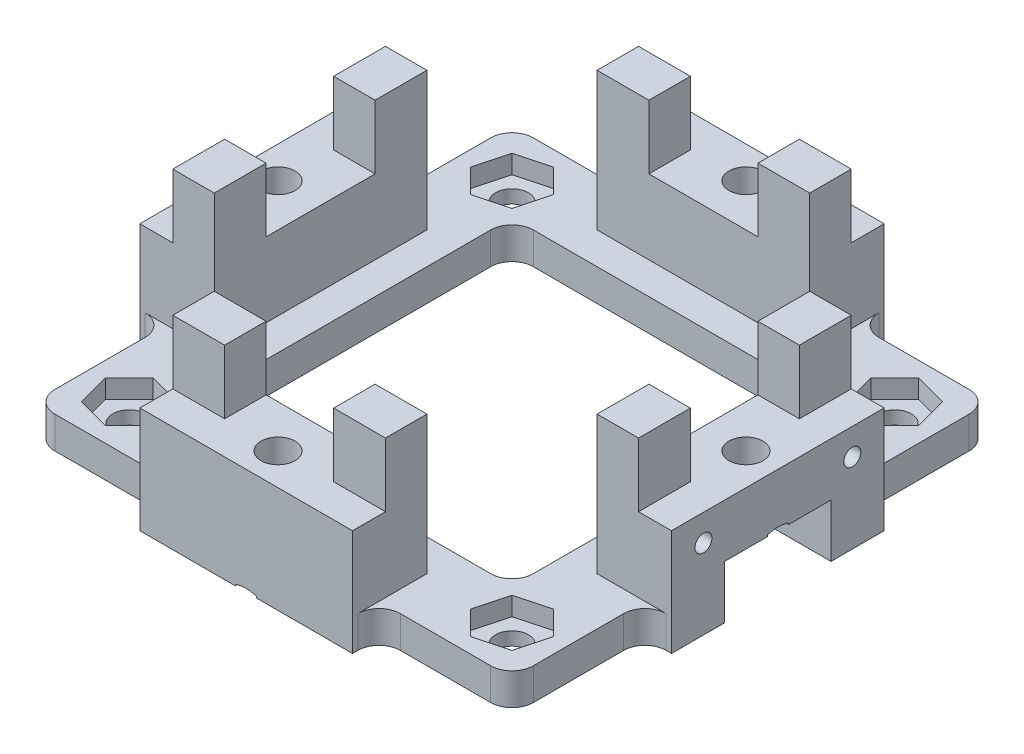
SolidWorks part; units mm, degrees
ref_plane "Front Plane" through (0, 0, 0) normal (0, 0, 1) x (1, 0, 0)
ref_plane "Top Plane" through (0, 0, 0) normal (0, 1, 0) x (1, 0, 0)
ref_plane "Right Plane" through (0, 0, 0) normal (1, 0, 0) x (0, 0, -1)
sketch "Sketch1" plane through (0, 0, 0) normal (0, 1, 0) x (1, 0, 0)
  line L0 (-10, 22.5) -> (-10, 25)
  line L1 (-15, -15) -> (15, -15)
  line L2 (-15, -15) -> (-15, 15)
  line L3 (-15, 15) -> (15, 15)
  line L4 (15, -15) -> (15, 15)
  line L5 (-15, -15) -> (15, 15) construction
  line L6 (-15, 15) -> (15, -15) construction
  line L7 (-22.5, -22.5) -> (-10, -22.5)
  line L8 (-22.5, -22.5) -> (-22.5, -10)
  line L9 (-22.5, 22.5) -> (-10, 22.5)
  line L10 (22.5, -22.5) -> (22.5, -10)
  line L11 (-22.5, -22.5) -> (22.5, 22.5) construction
  line L12 (-22.5, 22.5) -> (22.5, -22.5) construction
  line L13 (-10, 25) -> (10, 25)
  line L14 (10, 25) -> (10, 22.5)
  line L15 (0, 0) -> (0, 25) construction
  line L16 (22.5, 10) -> (25, 10)
  line L17 (25, 10) -> (25, -10)
  line L18 (25, -10) -> (22.5, -10)
  line L19 (0, 0) -> (25, 0) construction
  line L20 (10, -22.5) -> (10, -25)
  line L21 (10, -25) -> (-10, -25)
  line L22 (-10, -25) -> (-10, -22.5)
  line L23 (0, 0) -> (0, -25) construction
  line L24 (-22.5, -10) -> (-25, -10)
  line L25 (-25, -10) -> (-25, 10)
  line L26 (-25, 10) -> (-22.5, 10)
  line L27 (0, 0) -> (-25, 0) construction
  line L28 (-22.5, 10) -> (-22.5, 22.5)
  line L29 (10, 22.5) -> (22.5, 22.5)
  line L30 (22.5, 10) -> (22.5, 22.5)
  line L31 (10, -22.5) -> (22.5, -22.5)
  point P0 (0, 0)
  point P6 (0, 0)
  point P35 (0, 0)
  dimension "D1" = 30
  dimension "D2" = 45
  dimension "D3" = 20
  dimension "D4" = 25
extrude "Boss-Extrude1" add sketch "Sketch1" along normal blind 3
sketch "Sketch2" plane through (0, 3, 0) normal (0, 1, 0) x (1, 0, 0)
  line L1 (-10, 25) -> (10, 25)
  line L2 (-10, 25) -> (-10, 18)
  line L3 (-10, 18) -> (10, 18)
  line L4 (10, 25) -> (10, 18)
  line L5 (10, 22.5) -> (10, 25) construction
  line L6 (25, 10) -> (25, -10)
  line L7 (25, 10) -> (18, 10)
  line L8 (18, 10) -> (18, -10)
  line L9 (25, -10) -> (18, -10)
  line L10 (10, -25) -> (-10, -25)
  line L11 (10, -25) -> (10, -18)
  line L12 (10, -18) -> (-10, -18)
  line L13 (-10, -25) -> (-10, -18)
  line L14 (-25, -10) -> (-25, 10)
  line L15 (-25, -10) -> (-18, -10)
  line L16 (-18, -10) -> (-18, 10)
  line L17 (-25, 10) -> (-18, 10)
  line L18 (15, 15) -> (-15, 15) construction
  point P24 (0, 0)
  dimension "D2" = 3
  dimension "D1" = 4
extrude "Boss-Extrude2" add sketch "Sketch2" along normal offset from surface (7 mm away) 10 up to face at (0, 0, 0)
sketch "Sketch3" plane through (0, 10, 0) normal (0, 1, 0) x (1, 0, 0)
  line L0 (-10, 22.5) -> (-10, 18) construction
  line L1 (-10, 21.9) -> (-5.125, 21.9)
  line L2 (-10, 21.9) -> (-10, 18)
  line L3 (-10, 18) -> (-5.125, 18)
  line L4 (-5.125, 21.9) -> (-5.125, 18)
  line L5 (-10, 18) -> (10, 18) construction
  line L6 (0, 0) -> (0, 25) construction
  line L7 (10, 25) -> (-10, 25) construction
  line L8 (5.125, 21.9) -> (5.125, 18)
  line L9 (10, 18) -> (5.125, 18)
  line L10 (10, 21.9) -> (10, 18)
  line L11 (10, 21.9) -> (5.125, 21.9)
  line L12 (21.9, 10) -> (21.9, 5.125)
  line L13 (21.9, 10) -> (18, 10)
  line L14 (18, 10) -> (18, 5.125)
  line L15 (21.9, 5.125) -> (18, 5.125)
  line L16 (21.9, -5.125) -> (18, -5.125)
  line L17 (18, -10) -> (18, -5.125)
  line L18 (21.9, -10) -> (18, -10)
  line L19 (21.9, -10) -> (21.9, -5.125)
  line L20 (10, -21.9) -> (5.125, -21.9)
  line L21 (10, -21.9) -> (10, -18)
  line L22 (10, -18) -> (5.125, -18)
  line L23 (5.125, -21.9) -> (5.125, -18)
  line L24 (-5.125, -21.9) -> (-5.125, -18)
  line L25 (-10, -18) -> (-5.125, -18)
  line L26 (-10, -21.9) -> (-10, -18)
  line L27 (-10, -21.9) -> (-5.125, -21.9)
  line L28 (-21.9, -10) -> (-21.9, -5.125)
  line L29 (-21.9, -10) -> (-18, -10)
  line L30 (-18, -10) -> (-18, -5.125)
  line L31 (-21.9, -5.125) -> (-18, -5.125)
  line L32 (-21.9, 5.125) -> (-18, 5.125)
  line L33 (-18, 10) -> (-18, 5.125)
  line L34 (-21.9, 10) -> (-18, 10)
  line L35 (-21.9, 10) -> (-21.9, 5.125)
  line L36 (-10, 21.5) -> (10, 21.5) construction
  line L37 (-10, 25) -> (-10, 18) construction
  point P43 (0, 0)
  dimension "D1" = 10.25
  dimension "D2" = 4
  dimension "D3" = 3.9
extrude "Boss-Extrude3" add sketch "Sketch3" along normal blind 6
hole_wizard "CSK for M3 Flat Head Machine Screw1" positions "Sketch5" profile "Sketch4" countersink size "M3" standard "ANSI Metric"
sketch "Sketch5" plane through (0, 0, 0) normal (0, -1, 0) x (-1, 0, 0)
  line L0 (22, 0) -> (0, 0) construction
  point P0 (22, 0)
  point P12 (0, -22)
  point P13 (-22, 0)
  point P14 (0, 22)
  point P15 (0, 0)
  dimension "D1" = 22
sketch "Sketch4" plane through (-22, 0, 0) normal (1, 0, 0) x (0, 0, -1)
  line L0 (0, 0) -> (0, 20.9614)
  line L1 (0, 20.9614) -> (1.6, 20)
  line L2 (1.6, 20) -> (1.6, 1.7)
  line L3 (1.6, 1.7) -> (3.15, 0.15)
  line L4 (3.15, 0.15) -> (3.15, 0)
  line L6 (3.15, 0) -> (0, 0)
  line L7 (-1.6, 1.7) -> (-3.15, 0.15) construction
  line L10 (0, 20.9614) -> (-1.6, 20) construction
  line L11 (0, -6.35) -> (0, 107.95) construction
  dimension "Hole Dia." = 3.2
  dimension "Hole Depth" = 20
  dimension "C'Sink Dia." = 6.3
  dimension "C'Sink Angle" = 90
  dimension "Drill Angle" = 118
  dimension "Head Clearance" = 0.15
sketch "Sketch6" plane through (0, 3, 0) normal (0, 1, 0) x (1, 0, 0)
  line L0 (0, 0) -> (-22.5, 22.5) construction
  line L1 (-20.2454, 20.2454) -> (-21.0672, 17.1781)
  line L2 (-21.0672, 17.1781) -> (-18.8219, 14.9328)
  line L3 (-18.8219, 14.9328) -> (-15.7546, 15.7546)
  line L4 (-15.7546, 15.7546) -> (-14.9328, 18.8219)
  line L5 (-14.9328, 18.8219) -> (-17.1781, 21.0672)
  line L6 (-17.1781, 21.0672) -> (-20.2454, 20.2454)
  line L7 (-18, 18) -> (0, 18) construction
  line L8 (0, 18) -> (0, 0) construction
  line L9 (20.2454, 20.2454) -> (17.1781, 21.0672)
  line L10 (17.1781, 21.0672) -> (14.9328, 18.8219)
  line L11 (14.9328, 18.8219) -> (15.7546, 15.7546)
  line L12 (15.7546, 15.7546) -> (18.8219, 14.9328)
  line L13 (18.8219, 14.9328) -> (21.0672, 17.1781)
  line L14 (21.0672, 17.1781) -> (20.2454, 20.2454)
  line L15 (0, 0) -> (22.5, 22.5) construction
  line L16 (18, 18) -> (18, 0) construction
  line L17 (18, 0) -> (0, 0) construction
  line L18 (20.2454, -20.2454) -> (21.0672, -17.1781)
  line L19 (21.0672, -17.1781) -> (18.8219, -14.9328)
  line L20 (18.8219, -14.9328) -> (15.7546, -15.7546)
  line L21 (15.7546, -15.7546) -> (14.9328, -18.8219)
  line L22 (14.9328, -18.8219) -> (17.1781, -21.0672)
  line L23 (17.1781, -21.0672) -> (20.2454, -20.2454)
  line L24 (0, 0) -> (22.5, -22.5) construction
  line L25 (18, -18) -> (0, -18) construction
  line L26 (0, -18) -> (0, 0) construction
  line L27 (-20.2454, -20.2454) -> (-17.1781, -21.0672)
  line L28 (-17.1781, -21.0672) -> (-14.9328, -18.8219)
  line L29 (-14.9328, -18.8219) -> (-15.7546, -15.7546)
  line L30 (-15.7546, -15.7546) -> (-18.8219, -14.9328)
  line L31 (-18.8219, -14.9328) -> (-21.0672, -17.1781)
  line L32 (-21.0672, -17.1781) -> (-20.2454, -20.2454)
  line L33 (0, 0) -> (-22.5, -22.5) construction
  line L34 (-18, -18) -> (-18, 0) construction
  line L35 (-18, 0) -> (0, 0) construction
  circle A0 centre (-18, 18) radius 2.75 construction
  circle A1 centre (18, 18) radius 2.75 construction
  circle A2 centre (18, -18) radius 2.75 construction
  circle A3 centre (-18, -18) radius 2.75 construction
  point P46 (0, 0)
  dimension "D1" = 5.5
  dimension "D2" = 18
extrude "Cut-Extrude1" cut sketch "Sketch6" against normal blind 1.75
sketch "Sketch7" plane through (0, 3, 0) normal (0, 1, 0) x (1, 0, 0)
  line L0 (-20.2454, 20.2454) -> (-15.7546, 15.7546) construction
  line L1 (-15.7546, 15.7546) -> (-14.9328, 18.8219) construction
  line L2 (-15.7546, 15.7546) -> (-14.9328, 18.8219) construction
  line L3 (-18.8219, 14.9328) -> (-15.7546, 15.7546) construction
  line L4 (-18.8219, 14.9328) -> (-15.7546, 15.7546) construction
  line L5 (20.2454, 20.2454) -> (15.7546, 15.7546) construction
  line L6 (20.2454, -20.2454) -> (15.7546, -15.7546) construction
  line L7 (-20.2454, -20.2454) -> (-15.7546, -15.7546) construction
  circle A0 centre (-18, 18) radius 1.55
  circle A1 centre (18, 18) radius 1.55
  circle A2 centre (18, -18) radius 1.55
  circle A3 centre (-18, -18) radius 1.55
  point P28 (0, 0)
  dimension "D1" = 3.1
extrude "Cut-Extrude2" cut sketch "Sketch7" against normal through all
fillet "Fillet1" radius 2 16 edges at (-15, 1.5, -15) (-15, 1.5, 15) (15, 1.5, 15) (15, 1.5, -15) (-22.5, 1.5, -10) (22.5, 1.5, -10) (22.5, 1.5, 10) (10, 1.5, 22.5) (-10, 1.5, 22.5) (-22.5, 1.5, 10) (-22.5, 1.5, 22.5) (22.5, 1.5, 22.5) (22.5, 1.5, -22.5) (-22.5, 1.5, -22.5)
sketch "Sketch8" plane through (0, 0, 0) normal (0, -1, 0) x (1, 0, 0)
  line L0 (25, 10) -> (25, 0.9605) construction
  line L1 (15, -5) -> (25, -5)
  line L2 (15, -5) -> (15, 5)
  line L3 (15, 5) -> (25, 5)
  line L4 (25, -5) -> (25, 5)
  line L5 (15, -5) -> (25, 5) construction
  line L6 (15, 5) -> (25, -5) construction
  line L7 (15, 13) -> (15, -13) construction
  line L8 (20, 0) -> (0, 0) construction
  point P0 (20, 0)
  dimension "D1" = 10
extrude "Cut-Extrude3" cut sketch "Sketch8" against normal blind 5
hole_wizard "CSK for M3 Flat Head Machine Screw2" positions "Sketch10" profile "Sketch9" countersink size "M3" standard "ANSI Metric"
sketch "Sketch10" plane through (0, 5, 0) normal (0, -1, 0) x (-1, 0, 0)
  point P0 (-22, 0)
sketch "Sketch9" plane through (22, 5, 0) normal (1, 0, 0) x (0, 0, -1)
  line L0 (0, 0) -> (0, 20.9614)
  line L1 (0, 20.9614) -> (1.6, 20)
  line L2 (1.6, 20) -> (1.6, 1.7)
  line L3 (1.6, 1.7) -> (3.15, 0.15)
  line L4 (3.15, 0.15) -> (3.15, 0)
  line L6 (3.15, 0) -> (0, 0)
  line L7 (-1.6, 1.7) -> (-3.15, 0.15) construction
  line L10 (0, 20.9614) -> (-1.6, 20) construction
  line L11 (0, -6.35) -> (0, 107.95) construction
  dimension "Hole Dia." = 3.2
  dimension "Hole Depth" = 20
  dimension "C'Sink Dia." = 6.3
  dimension "C'Sink Angle" = 90
  dimension "Drill Angle" = 118
  dimension "Head Clearance" = 0.15
sketch "Sketch11" plane through (25, 0, 0) normal (1, 0, 0) x (0, 0, -1)
  line L0 (0, 0) -> (0, 19.1608) construction
  line L1 (13, 0) -> (-13, 0) construction
  circle A0 centre (7, 7.5) radius 0.8
  circle A1 centre (-7, 7.5) radius 0.8
  dimension "D2" = 1.6
  dimension "D1" = 7
  dimension "D3" = 7.5
extrude "Cut-Extrude4" cut sketch "Sketch11" against normal blind 7
